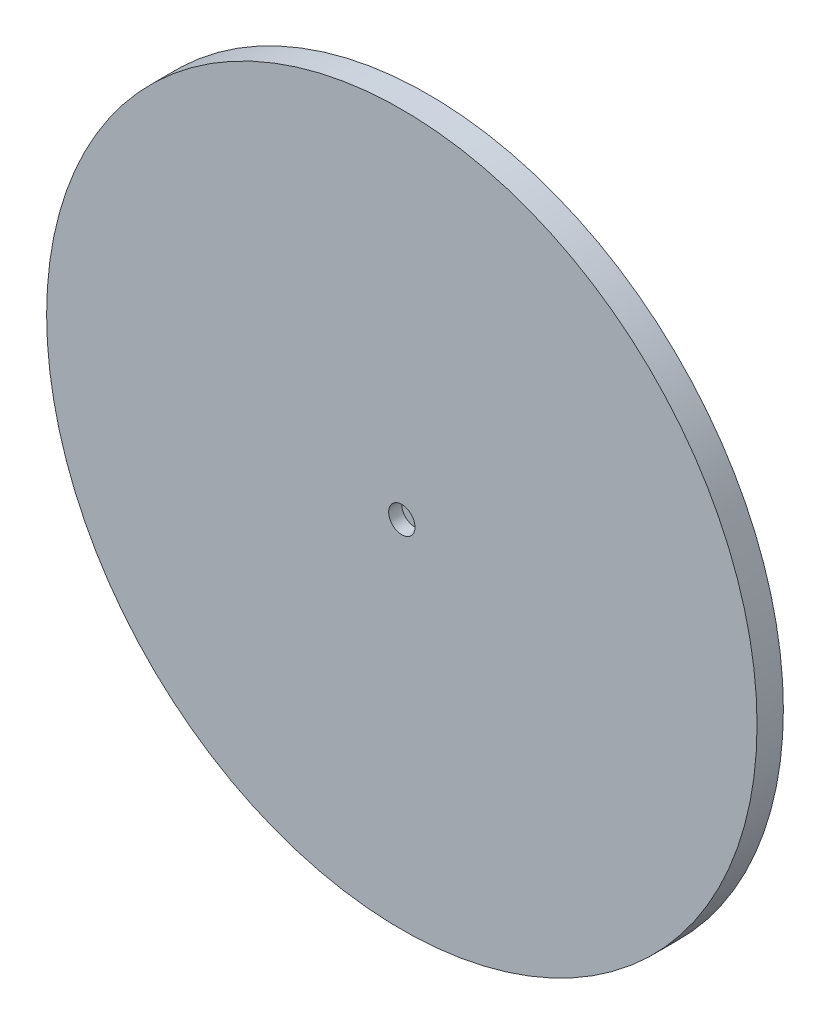
SolidWorks part; units mm, degrees
ref_plane "Plano frontal" through (0, 0, 0) normal (0, 0, 1) x (1, 0, 0)
ref_plane "Plano superior" through (0, 0, 0) normal (0, 1, 0) x (1, 0, 0)
ref_plane "Plano direito" through (0, 0, 0) normal (1, 0, 0) x (0, 0, -1)
sketch "Esboço1" plane through (0, 0, 0) normal (0, 0, 1) x (1, 0, 0)
  circle A0 centre (0, 0) radius 27
extrude "Ressalto-extrusão1" add sketch "Esboço1" along normal blind 2
sketch "Esboço3" plane through (0, 0, 0) normal (0, 0, -1) x (-1, 0, 0)
  circle A0 centre (0, 0) radius 5
extrude "Ressalto-extrusão2" add sketch "Esboço3" along normal blind 1
sketch "Esboço4" plane through (0, 0, 2) normal (0, 0, 1) x (1, 0, 0)
  circle A0 centre (0, 0) radius 1
extrude "Corte-extrusão1" cut sketch "Esboço4" against normal blind 1
